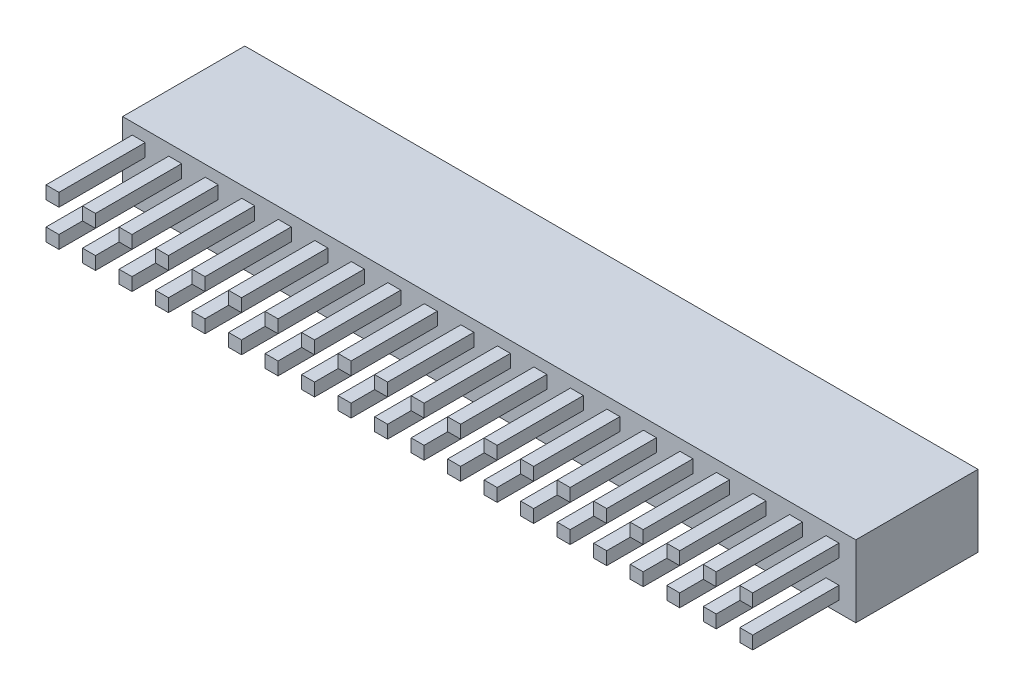
SolidWorks part; units mm, degrees
ref_plane "前视基准面" through (0, 0, 0) normal (0, 0, 1) x (1, 0, 0)
ref_plane "上视基准面" through (0, 0, 0) normal (0, 1, 0) x (1, 0, 0)
ref_plane "右视基准面" through (0, 0, 0) normal (1, 0, 0) x (0, 0, -1)
other "Configuration Table"
sketch "草图1" plane through (0, 0, 0) normal (0, 0, 1) x (1, 0, 0)
  line L1 (-87.7344, 58.2747) -> (-36.7344, 58.2747)
  line L2 (-87.7344, 58.2747) -> (-87.7344, 53.2747)
  line L3 (-87.7344, 53.2747) -> (-36.7344, 53.2747)
  line L4 (-36.7344, 58.2747) -> (-36.7344, 53.2747)
  dimension "D1" = 51
  dimension "D2" = 5
extrude "凸台-拉伸1" add sketch "草图1" along normal blind 8.5
sketch "草图3" plane through (0, 0, 8.5) normal (0, 0, 1) x (1, 0, 0)
  line L0 (-84.5244, 57.4947) -> (-84.5244, 56.5947)
  line L1 (-87.0644, 57.4947) -> (-86.1644, 57.4947)
  line L2 (-87.0644, 57.4947) -> (-87.0644, 56.5947)
  line L3 (-87.0644, 56.5947) -> (-86.1644, 56.5947)
  line L4 (-86.1644, 57.4947) -> (-86.1644, 56.5947)
  line L5 (-84.5244, 57.4947) -> (-83.6244, 57.4947)
  line L6 (-83.6244, 57.4947) -> (-83.6244, 56.5947)
  line L7 (-84.5244, 56.5947) -> (-83.6244, 56.5947)
  line L8 (-81.9844, 57.4947) -> (-81.9844, 56.5947)
  line L9 (-81.9844, 57.4947) -> (-81.0844, 57.4947)
  line L10 (-81.0844, 57.4947) -> (-81.0844, 56.5947)
  line L11 (-81.9844, 56.5947) -> (-81.0844, 56.5947)
  line L12 (-79.4444, 57.4947) -> (-79.4444, 56.5947)
  line L13 (-79.4444, 57.4947) -> (-78.5444, 57.4947)
  line L14 (-78.5444, 57.4947) -> (-78.5444, 56.5947)
  line L15 (-79.4444, 56.5947) -> (-78.5444, 56.5947)
  line L16 (-76.9044, 57.4947) -> (-76.9044, 56.5947)
  line L17 (-76.9044, 57.4947) -> (-76.0044, 57.4947)
  line L18 (-76.0044, 57.4947) -> (-76.0044, 56.5947)
  line L19 (-76.9044, 56.5947) -> (-76.0044, 56.5947)
  line L20 (-74.3644, 57.4947) -> (-74.3644, 56.5947)
  line L21 (-74.3644, 57.4947) -> (-73.4644, 57.4947)
  line L22 (-73.4644, 57.4947) -> (-73.4644, 56.5947)
  line L23 (-74.3644, 56.5947) -> (-73.4644, 56.5947)
  line L24 (-71.8244, 57.4947) -> (-71.8244, 56.5947)
  line L25 (-71.8244, 57.4947) -> (-70.9244, 57.4947)
  line L26 (-70.9244, 57.4947) -> (-70.9244, 56.5947)
  line L27 (-71.8244, 56.5947) -> (-70.9244, 56.5947)
  line L28 (-69.2844, 57.4947) -> (-69.2844, 56.5947)
  line L29 (-69.2844, 57.4947) -> (-68.3844, 57.4947)
  line L30 (-68.3844, 57.4947) -> (-68.3844, 56.5947)
  line L31 (-69.2844, 56.5947) -> (-68.3844, 56.5947)
  line L32 (-66.7444, 57.4947) -> (-66.7444, 56.5947)
  line L33 (-66.7444, 57.4947) -> (-65.8444, 57.4947)
  line L34 (-65.8444, 57.4947) -> (-65.8444, 56.5947)
  line L35 (-66.7444, 56.5947) -> (-65.8444, 56.5947)
  line L36 (-64.2044, 57.4947) -> (-64.2044, 56.5947)
  line L37 (-64.2044, 57.4947) -> (-63.3044, 57.4947)
  line L38 (-63.3044, 57.4947) -> (-63.3044, 56.5947)
  line L39 (-64.2044, 56.5947) -> (-63.3044, 56.5947)
  line L40 (-61.6644, 57.4947) -> (-61.6644, 56.5947)
  line L41 (-61.6644, 57.4947) -> (-60.7644, 57.4947)
  line L42 (-60.7644, 57.4947) -> (-60.7644, 56.5947)
  line L43 (-61.6644, 56.5947) -> (-60.7644, 56.5947)
  line L44 (-59.1244, 57.4947) -> (-59.1244, 56.5947)
  line L45 (-59.1244, 57.4947) -> (-58.2244, 57.4947)
  line L46 (-58.2244, 57.4947) -> (-58.2244, 56.5947)
  line L47 (-59.1244, 56.5947) -> (-58.2244, 56.5947)
  line L48 (-56.5844, 57.4947) -> (-56.5844, 56.5947)
  line L49 (-56.5844, 57.4947) -> (-55.6844, 57.4947)
  line L50 (-55.6844, 57.4947) -> (-55.6844, 56.5947)
  line L51 (-56.5844, 56.5947) -> (-55.6844, 56.5947)
  line L52 (-54.0444, 57.4947) -> (-54.0444, 56.5947)
  line L53 (-54.0444, 57.4947) -> (-53.1444, 57.4947)
  line L54 (-53.1444, 57.4947) -> (-53.1444, 56.5947)
  line L55 (-54.0444, 56.5947) -> (-53.1444, 56.5947)
  line L56 (-51.5044, 57.4947) -> (-51.5044, 56.5947)
  line L57 (-51.5044, 57.4947) -> (-50.6044, 57.4947)
  line L58 (-50.6044, 57.4947) -> (-50.6044, 56.5947)
  line L59 (-51.5044, 56.5947) -> (-50.6044, 56.5947)
  line L60 (-48.9644, 57.4947) -> (-48.9644, 56.5947)
  line L61 (-48.9644, 57.4947) -> (-48.0644, 57.4947)
  line L62 (-48.0644, 57.4947) -> (-48.0644, 56.5947)
  line L63 (-48.9644, 56.5947) -> (-48.0644, 56.5947)
  line L64 (-46.4244, 57.4947) -> (-46.4244, 56.5947)
  line L65 (-46.4244, 57.4947) -> (-45.5244, 57.4947)
  line L66 (-45.5244, 57.4947) -> (-45.5244, 56.5947)
  line L67 (-46.4244, 56.5947) -> (-45.5244, 56.5947)
  line L68 (-43.8844, 57.4947) -> (-43.8844, 56.5947)
  line L69 (-43.8844, 57.4947) -> (-42.9844, 57.4947)
  line L70 (-42.9844, 57.4947) -> (-42.9844, 56.5947)
  line L71 (-43.8844, 56.5947) -> (-42.9844, 56.5947)
  line L72 (-41.3444, 57.4947) -> (-41.3444, 56.5947)
  line L73 (-41.3444, 57.4947) -> (-40.4444, 57.4947)
  line L74 (-40.4444, 57.4947) -> (-40.4444, 56.5947)
  line L75 (-41.3444, 56.5947) -> (-40.4444, 56.5947)
  line L76 (-38.8044, 57.4947) -> (-38.8044, 56.5947)
  line L77 (-38.8044, 57.4947) -> (-37.9044, 57.4947)
  line L78 (-37.9044, 57.4947) -> (-37.9044, 56.5947)
  line L79 (-38.8044, 56.5947) -> (-37.9044, 56.5947)
  line L80 (-84.5244, 54.9547) -> (-84.5244, 54.0547)
  line L81 (-84.5244, 54.9547) -> (-83.6244, 54.9547)
  line L82 (-83.6244, 54.9547) -> (-83.6244, 54.0547)
  line L83 (-84.5244, 54.0547) -> (-83.6244, 54.0547)
  line L84 (-81.9844, 54.9547) -> (-81.9844, 54.0547)
  line L85 (-81.9844, 54.9547) -> (-81.0844, 54.9547)
  line L86 (-81.0844, 54.9547) -> (-81.0844, 54.0547)
  line L87 (-81.9844, 54.0547) -> (-81.0844, 54.0547)
  line L88 (-79.4444, 54.9547) -> (-79.4444, 54.0547)
  line L89 (-79.4444, 54.9547) -> (-78.5444, 54.9547)
  line L90 (-78.5444, 54.9547) -> (-78.5444, 54.0547)
  line L91 (-79.4444, 54.0547) -> (-78.5444, 54.0547)
  line L92 (-76.9044, 54.9547) -> (-76.9044, 54.0547)
  line L93 (-76.9044, 54.9547) -> (-76.0044, 54.9547)
  line L94 (-76.0044, 54.9547) -> (-76.0044, 54.0547)
  line L95 (-76.9044, 54.0547) -> (-76.0044, 54.0547)
  line L96 (-74.3644, 54.9547) -> (-74.3644, 54.0547)
  line L97 (-74.3644, 54.9547) -> (-73.4644, 54.9547)
  line L98 (-73.4644, 54.9547) -> (-73.4644, 54.0547)
  line L99 (-74.3644, 54.0547) -> (-73.4644, 54.0547)
  line L100 (-71.8244, 54.9547) -> (-71.8244, 54.0547)
  line L101 (-71.8244, 54.9547) -> (-70.9244, 54.9547)
  line L102 (-70.9244, 54.9547) -> (-70.9244, 54.0547)
  line L103 (-71.8244, 54.0547) -> (-70.9244, 54.0547)
  line L104 (-69.2844, 54.9547) -> (-69.2844, 54.0547)
  line L105 (-69.2844, 54.9547) -> (-68.3844, 54.9547)
  line L106 (-68.3844, 54.9547) -> (-68.3844, 54.0547)
  line L107 (-69.2844, 54.0547) -> (-68.3844, 54.0547)
  line L108 (-66.7444, 54.9547) -> (-66.7444, 54.0547)
  line L109 (-66.7444, 54.9547) -> (-65.8444, 54.9547)
  line L110 (-65.8444, 54.9547) -> (-65.8444, 54.0547)
  line L111 (-66.7444, 54.0547) -> (-65.8444, 54.0547)
  line L112 (-64.2044, 54.9547) -> (-64.2044, 54.0547)
  line L113 (-64.2044, 54.9547) -> (-63.3044, 54.9547)
  line L114 (-63.3044, 54.9547) -> (-63.3044, 54.0547)
  line L115 (-64.2044, 54.0547) -> (-63.3044, 54.0547)
  line L116 (-61.6644, 54.9547) -> (-61.6644, 54.0547)
  line L117 (-61.6644, 54.9547) -> (-60.7644, 54.9547)
  line L118 (-60.7644, 54.9547) -> (-60.7644, 54.0547)
  line L119 (-61.6644, 54.0547) -> (-60.7644, 54.0547)
  line L120 (-59.1244, 54.9547) -> (-59.1244, 54.0547)
  line L121 (-59.1244, 54.9547) -> (-58.2244, 54.9547)
  line L122 (-58.2244, 54.9547) -> (-58.2244, 54.0547)
  line L123 (-59.1244, 54.0547) -> (-58.2244, 54.0547)
  line L124 (-56.5844, 54.9547) -> (-56.5844, 54.0547)
  line L125 (-56.5844, 54.9547) -> (-55.6844, 54.9547)
  line L126 (-55.6844, 54.9547) -> (-55.6844, 54.0547)
  line L127 (-56.5844, 54.0547) -> (-55.6844, 54.0547)
  line L128 (-54.0444, 54.9547) -> (-54.0444, 54.0547)
  line L129 (-54.0444, 54.9547) -> (-53.1444, 54.9547)
  line L130 (-53.1444, 54.9547) -> (-53.1444, 54.0547)
  line L131 (-54.0444, 54.0547) -> (-53.1444, 54.0547)
  line L132 (-51.5044, 54.9547) -> (-51.5044, 54.0547)
  line L133 (-51.5044, 54.9547) -> (-50.6044, 54.9547)
  line L134 (-50.6044, 54.9547) -> (-50.6044, 54.0547)
  line L135 (-51.5044, 54.0547) -> (-50.6044, 54.0547)
  line L136 (-48.9644, 54.9547) -> (-48.9644, 54.0547)
  line L137 (-48.9644, 54.9547) -> (-48.0644, 54.9547)
  line L138 (-48.0644, 54.9547) -> (-48.0644, 54.0547)
  line L139 (-48.9644, 54.0547) -> (-48.0644, 54.0547)
  line L140 (-46.4244, 54.9547) -> (-46.4244, 54.0547)
  line L141 (-46.4244, 54.9547) -> (-45.5244, 54.9547)
  line L142 (-45.5244, 54.9547) -> (-45.5244, 54.0547)
  line L143 (-46.4244, 54.0547) -> (-45.5244, 54.0547)
  line L144 (-43.8844, 54.9547) -> (-43.8844, 54.0547)
  line L145 (-43.8844, 54.9547) -> (-42.9844, 54.9547)
  line L146 (-42.9844, 54.9547) -> (-42.9844, 54.0547)
  line L147 (-43.8844, 54.0547) -> (-42.9844, 54.0547)
  line L148 (-41.3444, 54.9547) -> (-41.3444, 54.0547)
  line L149 (-41.3444, 54.9547) -> (-40.4444, 54.9547)
  line L150 (-40.4444, 54.9547) -> (-40.4444, 54.0547)
  line L151 (-41.3444, 54.0547) -> (-40.4444, 54.0547)
  line L152 (-38.8044, 54.9547) -> (-38.8044, 54.0547)
  line L153 (-38.8044, 54.9547) -> (-37.9044, 54.9547)
  line L154 (-37.9044, 54.9547) -> (-37.9044, 54.0547)
  line L155 (-38.8044, 54.0547) -> (-37.9044, 54.0547)
  line L156 (-87.0644, 54.9547) -> (-87.0644, 54.0547)
  line L157 (-87.0644, 54.9547) -> (-86.1644, 54.9547)
  line L158 (-86.1644, 54.9547) -> (-86.1644, 54.0547)
  line L159 (-87.0644, 54.0547) -> (-86.1644, 54.0547)
  dimension "D1" = 20
  dimension "D2" = 2
extrude "凸台-拉伸2" add sketch "草图3" along normal blind 6
